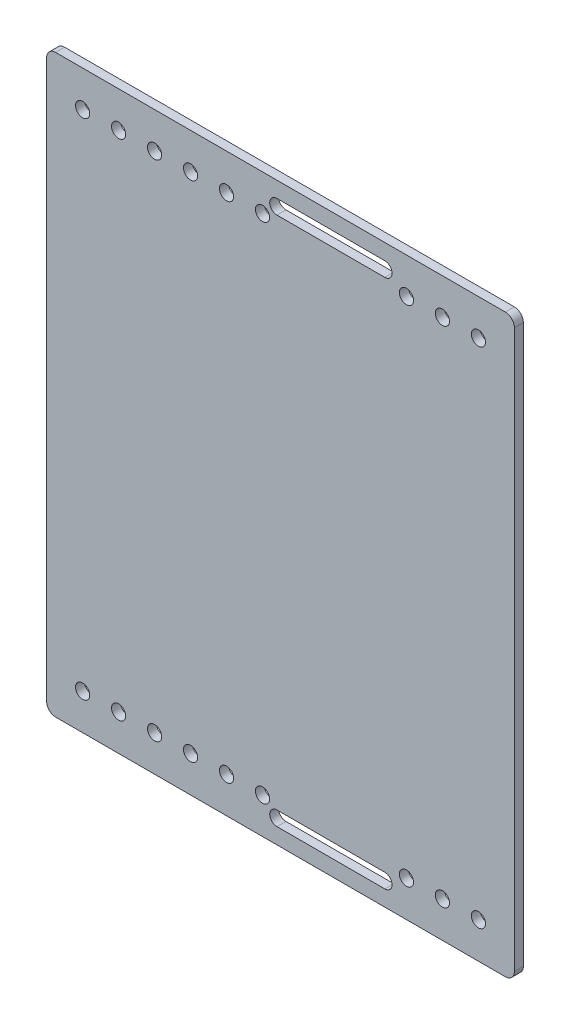
SolidWorks part; units mm, degrees
ref_plane "Front Plane" through (0, 0, 0) normal (0, 0, 1) x (1, 0, 0)
ref_plane "Top Plane" through (0, 0, 0) normal (0, 1, 0) x (1, 0, 0)
ref_plane "Right Plane" through (0, 0, 0) normal (1, 0, 0) x (0, 0, -1)
sketch "Sketch1" plane through (0, 0, 0) normal (0, 0, 1) x (1, 0, 0)
  line B0 (-227.3941, -79.6073) -> (-386.1441, -79.6073)
  line B1 (-224.2191, -76.4323) -> (-224.2191, 120.4177)
  line B2 (-227.3941, 123.5927) -> (-386.1441, 123.5927)
  line B3 (-389.3191, -76.4323) -> (-389.3191, 120.4177)
  arc B4 (-227.3941, -79.6073) -> (-224.2191, -76.4323) centre (-227.3941, -76.4323) ccw
  arc B5 (-224.2191, 120.4177) -> (-227.3941, 123.5927) centre (-227.3941, 120.4177) ccw
  arc B6 (-386.1441, 123.5927) -> (-389.3191, 120.4177) centre (-386.1441, 120.4177) ccw
  arc B7 (-386.1441, -79.6073) -> (-389.3191, -76.4323) centre (-386.1441, -76.4323) cw
  line B8 (-308.0391, 118.0047) -> (-269.9391, 118.0047)
  arc B9 (-269.9391, 112.9247) -> (-269.9391, 118.0047) centre (-269.9391, 115.4647) ccw
  line B10 (-308.0391, 112.9247) -> (-269.9391, 112.9247)
  arc B11 (-308.0391, 118.0047) -> (-308.0391, 112.9247) centre (-308.0391, 115.4647) ccw
  line B12 (-308.0391, -68.9393) -> (-269.9391, -68.9393)
  arc B13 (-269.9391, -74.0193) -> (-269.9391, -68.9393) centre (-269.9391, -71.4793) ccw
  line B14 (-308.0391, -74.0193) -> (-269.9391, -74.0193)
  arc B15 (-308.0391, -68.9393) -> (-308.0391, -74.0193) centre (-308.0391, -71.4793) ccw
sketch_block_instance "Block-BottomBatteryPlate-1"
sketch_block "Block-BottomBatteryPlate" parameters "D1"=3.175
extrude "Boss-Extrude1" add sketch "Sketch1" along normal blind 3.175
sketch "Sketch3" plane through (0, 0, 3.175) normal (0, 0, 1) x (1, 0, 0)
  line L0 (-227.3941, 123.5927) -> (-386.1441, 123.5927) construction
  line L1 (-389.3191, 120.4177) -> (-389.3191, -76.4323) construction
  line L2 (-386.1441, -79.6073) -> (-227.3941, -79.6073) construction
  line L3 (-224.2191, -76.4323) -> (-224.2191, 120.4177) construction
  circle A0 centre (-376.6191, 110.8927) radius 2.505
  circle A1 centre (-376.6191, -66.9073) radius 2.505
  circle A2 centre (-363.9191, 110.8927) radius 2.505
  circle A3 centre (-363.9191, -66.9073) radius 2.505
  circle A4 centre (-351.2191, 110.8927) radius 2.505
  circle A5 centre (-351.2191, -66.9073) radius 2.505
  circle A6 centre (-338.5191, 110.8927) radius 2.505
  circle A7 centre (-338.5191, -66.9073) radius 2.505
  circle A8 centre (-325.8191, 110.8927) radius 2.505
  circle A9 centre (-325.8191, -66.9073) radius 2.505
  circle A10 centre (-313.1191, 110.8927) radius 2.505
  circle A11 centre (-313.1191, -66.9073) radius 2.505
  circle A12 centre (-236.9191, 110.8927) radius 2.505
  circle A13 centre (-236.9191, -66.9073) radius 2.505
  circle A14 centre (-249.6191, -66.9073) radius 2.505
  circle A15 centre (-249.6191, 110.8927) radius 2.505
  circle A16 centre (-262.3191, -66.9073) radius 2.505
  circle A17 centre (-262.3191, 110.8927) radius 2.505
  dimension "D1" = 5.01
  dimension "D6" = 5.01
  dimension "D8" = 5.01
  dimension "D13" = 5.01
  dimension "D2" = 12.7
  dimension "D3" = 12.7
  dimension "D4" = 12.7
  dimension "D5" = 12.7
  dimension "D9" = 12.7
  dimension "D10" = 12.7
  dimension "D11" = 12.7
  dimension "D12" = 12.7
  dimension "D7" = 6
  dimension "D14" = 3
extrude "Cut-Extrude4" cut sketch "Sketch3" against normal through all
